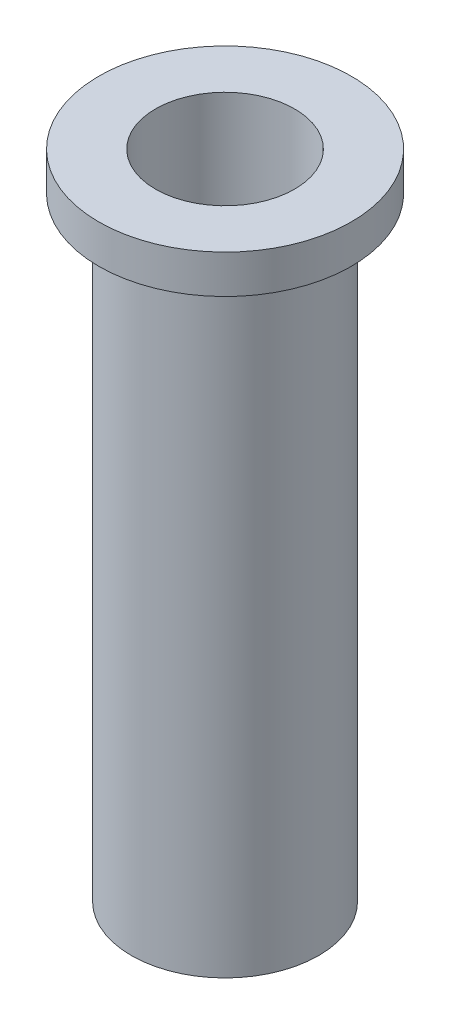
SolidWorks part; units mm, degrees
ref_plane "Front Plane" through (0, 0, 0) normal (0, 0, 1) x (1, 0, 0)
ref_plane "Top Plane" through (0, 0, 0) normal (0, 1, 0) x (1, 0, 0)
ref_plane "Right Plane" through (0, 0, 0) normal (1, 0, 0) x (0, 0, -1)
sketch "Sketch1" plane through (0, 0, 0) normal (0, 1, 0) x (1, 0, 0)
  circle A0 centre (0, 0) radius 7.3025
  dimension "D1" = 14.605
extrude "Boss-Extrude1" add sketch "Sketch1" along normal blind 50.8
sketch "Sketch2" plane through (0, 50.8, 0) normal (0, 1, 0) x (1, 0, 0)
  circle A0 centre (0, 0) radius 1.6129
  dimension "D1" = 3.2258
extrude "Cut-Extrude1" cut sketch "Sketch2" against normal up to surface (50.8 mm away) up to face at (0, 0, 7.3025)
ref_axis "Axis1" through (0, 34.671, 0) along (0, -1, 0)
sketch "Sketch3" plane through (0, 0, 0) normal (0, 0, 1) x (1, 0, 0)
  line L0 (-5.4229, 15.119) -> (-1.6129, 9.2157)
  line L2 (-1.6129, 50.8) -> (-1.6129, 0) construction
  line L3 (-1.6129, 9.2157) -> (-1.6129, 15.119)
  line L4 (-1.6129, 15.119) -> (-5.4229, 15.119)
  point P6 (0, 0)
  dimension "D1" = 3.81
revolve "Cut-Revolve1" cut sketch "Sketch3" angle 360 about axis through (0, 34.671, 0) along (0, -1, 0)
sketch "Sketch5" plane through (0, 0, 0) normal (1, 0, 0) x (0, 0, -1)
  line L1 (7.3025, 50.8) -> (9.8425, 50.8)
  line L2 (7.3025, 50.8) -> (7.3025, 47.8)
  line L3 (7.3025, 47.8) -> (9.8425, 47.8)
  line L4 (9.8425, 50.8) -> (9.8425, 47.8)
  dimension "D1" = 2.54
  dimension "D2" = 3
revolve "Revolve1" add sketch "Sketch5" angle 360 about axis through (0, 34.671, 0) along (0, -1, 0)
sketch "Sketch6" plane through (0, 50.8, 0) normal (0, 1, 0) x (1, 0, 0)
  circle A0 centre (0, 0) radius 5.4229
  dimension "D1" = 10.8458
extrude "Cut-Extrude3" cut sketch "Sketch6" against normal blind 35.6819
